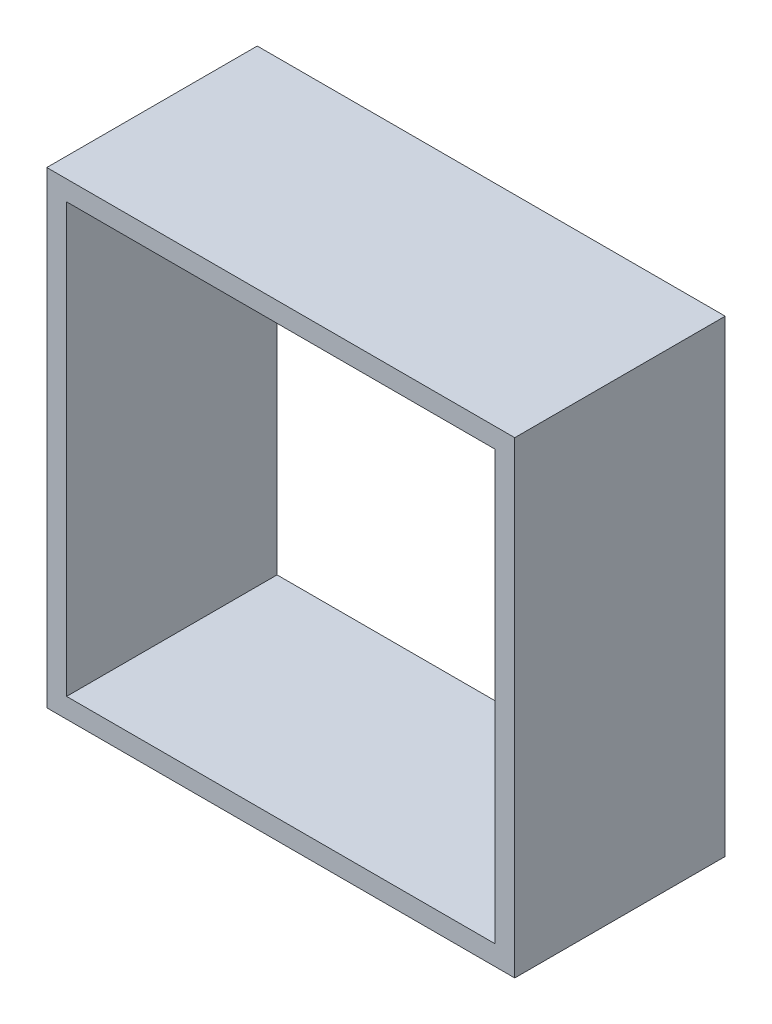
SolidWorks part; units mm, degrees
ref_plane "Front Plane" through (0, 0, 0) normal (0, 0, 1) x (1, 0, 0)
ref_plane "Top Plane" through (0, 0, 0) normal (0, 1, 0) x (1, 0, 0)
ref_plane "Right Plane" through (0, 0, 0) normal (1, 0, 0) x (0, 0, -1)
sketch "Sketch1" plane through (0, 0, 0) normal (0, 0, 1) x (1, 0, 0)
  line L1 (-9.45, -9.45) -> (9.45, -9.45)
  line L2 (-9.45, -9.45) -> (-9.45, 9.45)
  line L3 (-9.45, 9.45) -> (9.45, 9.45)
  line L4 (9.45, -9.45) -> (9.45, 9.45)
  line L5 (-9.45, -9.45) -> (9.45, 9.45) construction
  line L6 (-9.45, 9.45) -> (9.45, -9.45) construction
  line L7 (-8.65, -8.65) -> (8.65, -8.65)
  line L8 (-8.65, -8.65) -> (-8.65, 8.65)
  line L9 (-8.65, 8.65) -> (8.65, 8.65)
  line L10 (8.65, -8.65) -> (8.65, 8.65)
  line L11 (-8.65, -8.65) -> (8.65, 8.65) construction
  line L12 (-8.65, 8.65) -> (8.65, -8.65) construction
  point P0 (0, 0)
  point P6 (0, 0)
  dimension "D1" = 18.9
  dimension "D2" = 0.8
extrude "Boss-Extrude1" add sketch "Sketch1" along normal blind 8.5
